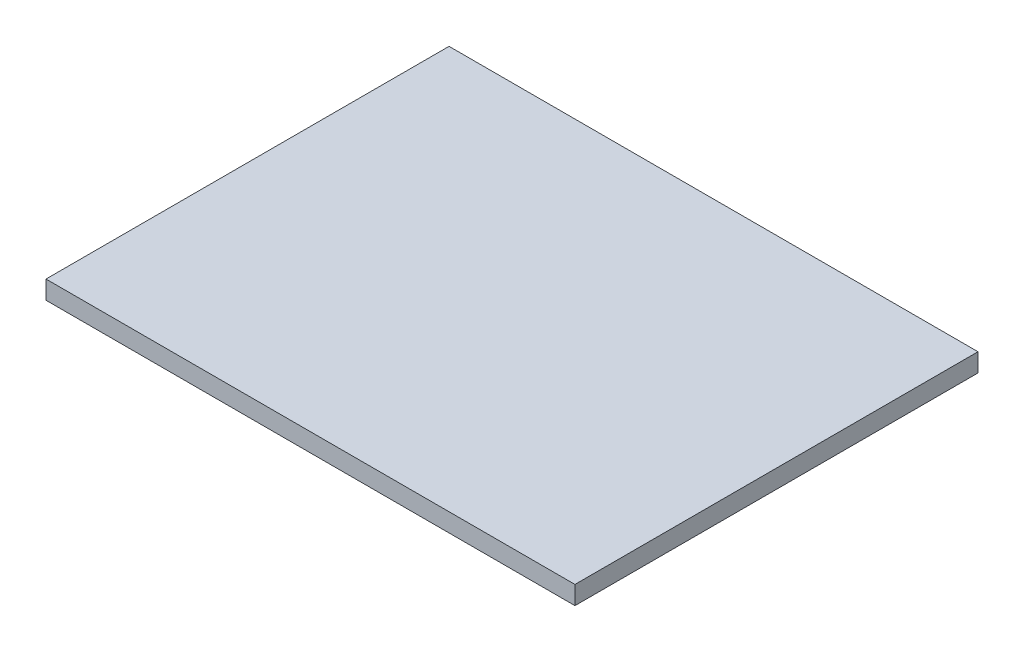
SolidWorks part; units mm, degrees
ref_plane "Front Plane" through (0, 0, 0) normal (0, 0, 1) x (1, 0, 0)
ref_plane "Top Plane" through (0, 0, 0) normal (0, 1, 0) x (1, 0, 0)
ref_plane "Right Plane" through (0, 0, 0) normal (1, 0, 0) x (0, 0, -1)
sketch "Sketch1" plane through (0, 0, 0) normal (0, 1, 0) x (1, 0, 0)
  line L1 (0, 0) -> (115, 0)
  line L2 (0, 0) -> (0, -87.6254)
  line L3 (0, -87.6254) -> (115, -87.6254)
  line L4 (115, 0) -> (115, -87.6254)
  dimension "D1" = 115
extrude "Boss-Extrude1" add sketch "Sketch1" along normal mid plane 4
